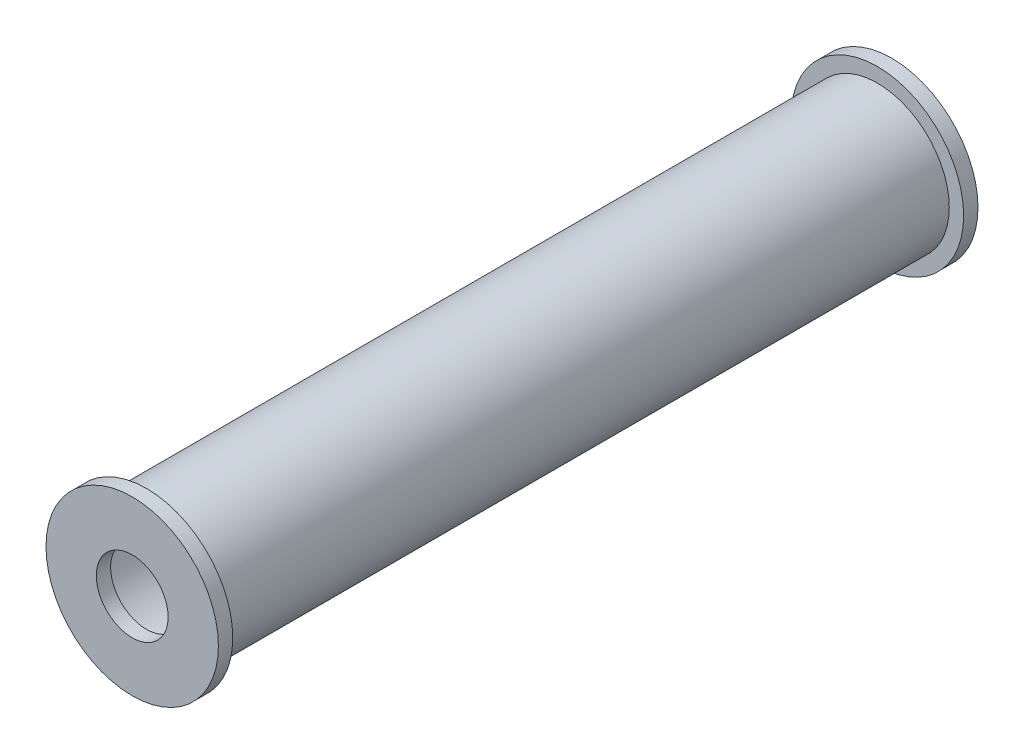
SolidWorks part; units mm, degrees
material "Plain Carbon Steel"
ref_plane "Спереди" through (0, 0, 0) normal (0, 0, 1) x (1, 0, 0)
ref_plane "Сверху" through (0, 0, 0) normal (0, 1, 0) x (1, 0, 0)
ref_plane "Справа" through (0, 0, 0) normal (1, 0, 0) x (0, 0, -1)
other "Configuration Table"
sketch "Sketch1" plane through (0, 0, 0) normal (0, 0, 1) x (1, 0, 0)
  circle A0 centre (0, 0) radius 5
  circle A1 centre (0, 0) radius 4.5
  dimension "D1" = 10
  dimension "D2" = 0.5
extrude "Boss-Extrude1" add sketch "Sketch1" along normal blind 50.8765
sketch "Sketch2" plane through (0, 0, 0) normal (0, 0, -1) x (-1, 0, 0)
  circle A0 centre (0, 0) radius 6
  circle A1 centre (0, 0) radius 2.5
  dimension "D1" = 5
  dimension "D2" = 12
extrude "Boss-Extrude2" add sketch "Sketch2" along normal blind 1
sketch "Sketch3" plane through (0, 0, 50.8765) normal (0, 0, 1) x (1, 0, 0)
  circle A0 centre (0, 0) radius 6
  circle A1 centre (0, 0) radius 2.5
extrude "Boss-Extrude3" add sketch "Sketch3" along normal blind 1
